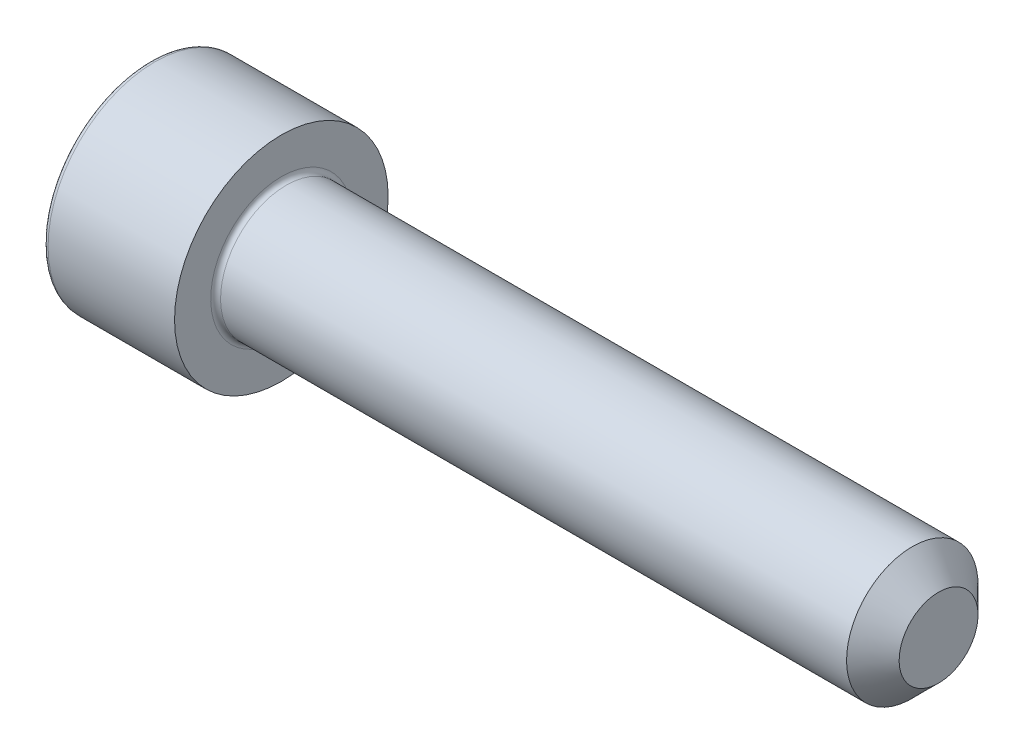
SolidWorks part; units mm, degrees
ref_plane "Спереди" through (0, 0, 0) normal (0, 0, 1) x (1, 0, 0)
ref_plane "Сверху" through (0, 0, 0) normal (0, 1, 0) x (1, 0, 0)
ref_plane "Справа" through (0, 0, 0) normal (1, 0, 0) x (0, 0, -1)
sketch "Эскиз1" plane through (0, 0, 0) normal (0, 0, 1) x (1, 0, 0)
  line L0 (0, 0) -> (0, 6.5)
  line L1 (0, 6.5) -> (8, 6.5)
  line L2 (8, 6.5) -> (8, 4)
  line L3 (8, 4) -> (48, 4)
  line L4 (48, 4) -> (48, 0)
  line L5 (48, 0) -> (0, 0) construction
  line L6 (0, 0) -> (48, 0)
  dimension "D1" = 13
  dimension "D2" = 8
  dimension "D3" = 8
  dimension "D4" = 40
revolve "Повернуть1" add sketch "Эскиз1" angle 360 about L5
cosmetic thread "Условное изображение резьбы1" parameters "D2"=6.619
sketch "Эскиз2" plane through (0, 0, 0) normal (-1, 0, 0) x (0, 0, 1)
  line L1 (-1.7321, 3) -> (-3.4641, 0)
  line L2 (-3.4641, 0) -> (-1.7321, -3)
  line L3 (-1.7321, -3) -> (1.7321, -3)
  line L4 (1.7321, -3) -> (3.4641, 0)
  line L5 (3.4641, 0) -> (1.7321, 3)
  line L6 (1.7321, 3) -> (-1.7321, 3)
  circle A0 centre (0, 0) radius 3 construction
  dimension "D1" = 6
extrude "Вырез-Вытянуть1" cut sketch "Эскиз2" against normal blind 2.5
fillet "Скругление1" radius 0.3 2 edges at (0, 6.5, 0) (8, 4, 0)
chamfer "Фаска1" distance 1.6 angle 45 1 edges at (48, 4, 0)
